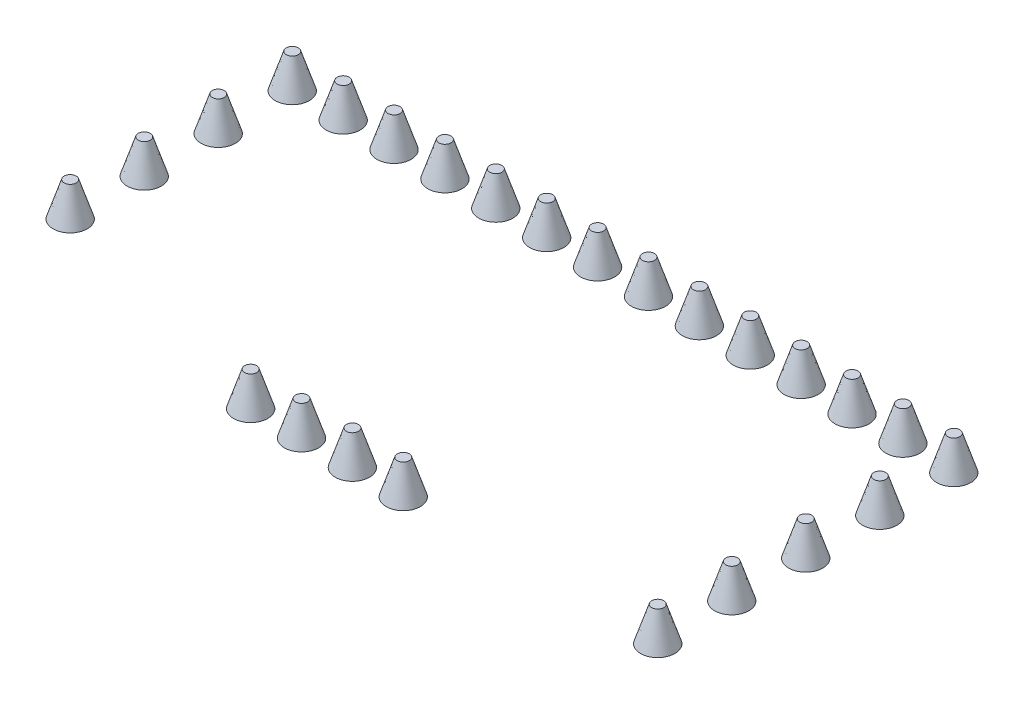
SolidWorks part; units mm, degrees
ref_plane "前视基准面" through (0, 0, 0) normal (0, 0, 1) x (1, 0, 0)
ref_plane "上视基准面" through (0, 0, 0) normal (0, 1, 0) x (1, 0, 0)
ref_plane "右视基准面" through (0, 0, 0) normal (1, 0, 0) x (0, 0, -1)
sketch "草图2" plane through (0, 0, 0) normal (0, 0, 1) x (1, 0, 0)
  line L0 (0, -0.5453) -> (0, 73.4547)
  line L1 (0, 73.4547) -> (13, 73.4547)
  line L2 (13, 73.4547) -> (37, -0.5453)
  line L3 (37, -0.5453) -> (0, -0.5453)
  dimension "D1" = 37
  dimension "D2" = 74
  dimension "D3" = 13
revolve "旋转1" add sketch "草图2" angle 360 about L0
sketch "草图4" plane through (0, 0, 0) normal (0, 1, 0) x (1, 0, 0)
  line L0 (0, 0) -> (0, -63.2129) construction
  line L1 (0, -40.7) -> (0, 40.7) construction
  line L2 (0, 0) -> (94.6609, 0) construction
pattern_linear "阵列(线性)3" count 4 spacing 160 along (0, 0, 1) of bodies 107
pattern_linear "阵列(线性)4" count 14 spacing 110 along (1, 0, 0) of bodies 107
pattern_linear "阵列(线性)5" count 5 spacing 160 along (0, 0, 1) of bodies 125
pattern_linear "阵列(线性)6" count 2 spacing 550 along (-1, 0, 0) of bodies 129
pattern_linear "阵列(线性)7" count 4 spacing 110 along (-1, 0, 0) of bodies 130
